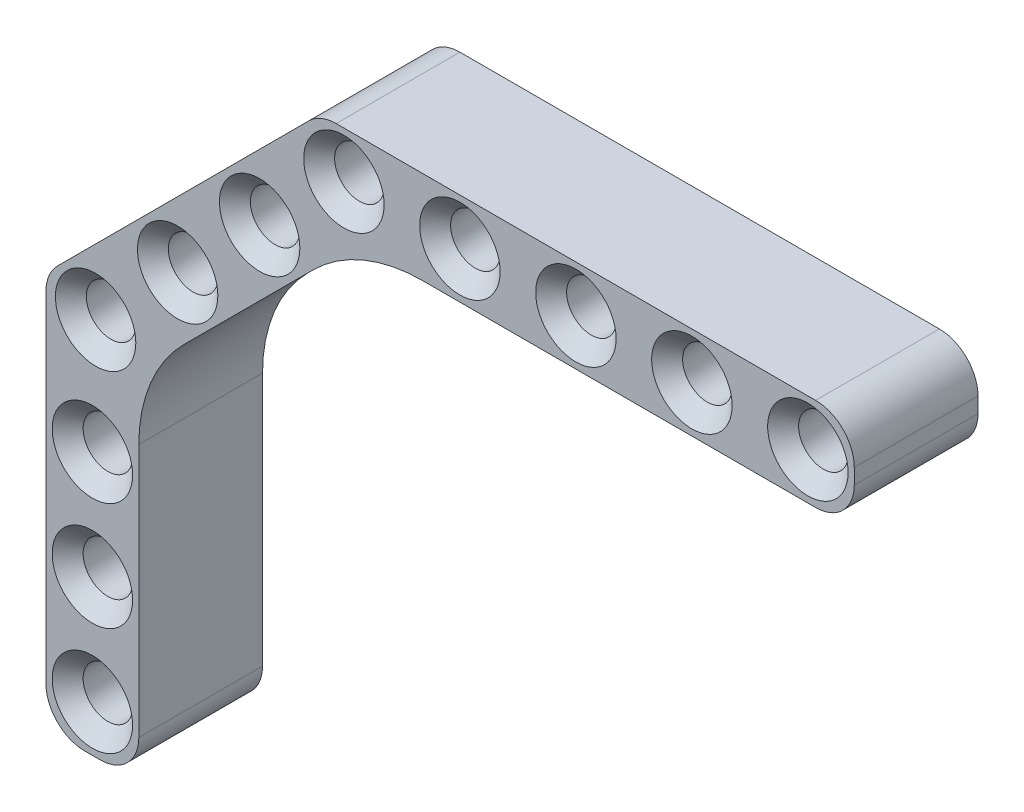
SolidWorks part; units mm, degrees
ref_plane "Front Plane" through (0, 0, 0) normal (0, 0, 1) x (1, 0, 0)
ref_plane "Top Plane" through (0, 0, 0) normal (0, 1, 0) x (1, 0, 0)
ref_plane "Right Plane" through (0, 0, 0) normal (1, 0, 0) x (0, 0, -1)
sketch "Sketch1" plane through (0, 0, 0) normal (0, 0, 1) x (1, 0, 0)
  line L1 (-0.5, 3) -> (30.5, 3)
  line L2 (-3, 0.5) -> (-3, -0.5)
  line L3 (-0.5, -3) -> (30.5, -3)
  line L4 (33, 0.5) -> (33, -0.5)
  circle A0 centre (0, 0) radius 1.6
  arc A1 (30.5, -3) -> (33, -0.5) centre (30.5, -0.5) ccw
  arc A2 (30.5, 3) -> (33, 0.5) centre (30.5, 0.5) cw
  arc A3 (-3, -0.5) -> (-0.5, -3) centre (-0.5, -0.5) ccw
  arc A4 (-0.5, 3) -> (-3, 0.5) centre (-0.5, 0.5) ccw
  circle A5 centre (7.5, 0) radius 1.6
  circle A6 centre (15, 0) radius 1.6
  circle A7 centre (22.5, 0) radius 1.6
  circle A8 centre (30, 0) radius 1.6
  point P8 (-3, 0)
  point P14 (-3, -3)
  point P17 (-3, 3)
  dimension "D1" = 3.2
  dimension "D4" = 2.5
  dimension "D2" = 6
  dimension "D3" = 3
  dimension "D6" = 7.5
  dimension "D5" = 5
extrude "Boss-Extrude1" add sketch "Sketch1" along normal blind 8
chamfer "Chamfer1" distance 1 angle 45 10 edges at (31.6, 0, 0) (31.6, 0, 8) (24.1, 0, 0) (24.1, 0, 8) (16.6, 0, 0) (16.6, 0, 8) (9.1, 0, 0) (9.1, 0, 8) (1.6, 0, 0) (1.6, 0, 8)
sketch "Sketch2" plane through (0, 0, 8) normal (0, 0, 1) x (1, 0, 0)
  line L0 (-2.2678, 2.2678) -> (-18.5292, -13.9937)
  line L1 (-18.5292, -17.5292) -> (-17.8221, -18.2363)
  line L2 (-14.2866, -18.2363) -> (0.9497, -3)
  line L4 (-0.5, -3) -> (30.5, -3) construction
  arc A0 (-0.5, 3) -> (-3, 0.5) centre (-0.5, 0.5) ccw construction
  circle A1 centre (-5.4477, -5.1548) radius 1.6
  circle A2 centre (-10.751, -10.4581) radius 1.6
  circle A3 centre (-16.0543, -15.7614) radius 1.6
  arc A4 (-18.5292, -13.9937) -> (-18.5292, -17.5292) centre (-16.7614, -15.7614) ccw
  arc A5 (-17.8221, -18.2363) -> (-14.2866, -18.2363) centre (-16.0543, -16.4685) ccw
  point P18 (-20.297, -15.7614)
  point P21 (-16.0543, -20.0041)
  arc M15 (-0.5, 3) -> (-3, 0.5) centre (-0.5, 0.5) ccw
  line M16 (-3, 0.5) -> (-3, -0.5)
  arc M17 (-3, -0.5) -> (-0.5, -3) centre (-0.5, -0.5) ccw
  line M18 (-0.5, -3) -> (30.5, -3)
  dimension "D3" = 3.2
  dimension "D8" = 2.5
  dimension "D1" = 6
  dimension "D2" = 45
  dimension "D4" = 3
  dimension "D5" = 7.5
  dimension "D7" = 3
  dimension "D6" = 3
extrude "Boss-Extrude3" add sketch "Sketch2" against normal blind 8 contours L1 A5 L2 L0 A4 A1 A2 A3 M18 M17 M16 M15
fillet "Fillet1" radius 10 1 edges at (0.9497, -3, 4)
chamfer "Chamfer2" distance 1 angle 45 6 edges at (-14.4543, -15.7614, 8) (-14.4543, -15.7614, 0) (-9.151, -10.4581, 8) (-9.151, -10.4581, 0) (-3.8477, -5.1548, 8) (-3.8477, -5.1548, 0)
sketch "Sketch3" plane through (0, 0, 8) normal (0, 0, 1) x (1, 0, 0)
  line L0 (-14.2866, -18.2363) -> (-1.9792, -5.9289) construction
  line L2 (-19.2614, -15.7614) -> (-19.2614, -37.7614)
  line L3 (-16.7614, -40.2614) -> (-15.7614, -40.2614)
  line L4 (-13.2614, -17.2112) -> (-13.2614, -37.7614)
  arc A0 (-18.5292, -13.9937) -> (-18.5292, -17.5292) centre (-16.7614, -15.7614) ccw construction
  circle A1 centre (-16.2614, -23.2614) radius 1.6
  circle A2 centre (-16.0543, -15.7614) radius 1.6 construction
  circle A3 centre (-16.2614, -30.2614) radius 1.6
  circle A4 centre (-16.2614, -37.2614) radius 1.6
  arc A5 (-19.2614, -37.7614) -> (-16.7614, -40.2614) centre (-16.7614, -37.7614) ccw
  arc A6 (-15.7614, -40.2614) -> (-13.2614, -37.7614) centre (-15.7614, -37.7614) ccw
  point P14 (-16.2614, -40.2614)
  point P20 (-19.2614, -40.2614)
  point P23 (-13.2614, -40.2614)
  arc M22 (-18.5292, -13.9937) -> (-18.5292, -17.5292) centre (-16.7614, -15.7614) ccw
  line M23 (-18.5292, -17.5292) -> (-17.8221, -18.2363)
  arc M24 (-17.8221, -18.2363) -> (-14.2866, -18.2363) centre (-16.0543, -16.4685) ccw
  line M25 (-14.2866, -18.2363) -> (-1.9792, -5.9289)
  dimension "D3" = 3.2
  dimension "D6" = 2.5
  dimension "D1" = 6
  dimension "D2" = 7.5
  dimension "D5" = 3
  dimension "D4" = 3
extrude "Boss-Extrude4" add sketch "Sketch3" against normal blind 8 contours L3 A6 L4 L2 A5 A1 A3 A4 M25 M24 M23 M22
chamfer "Chamfer5" distance 1 angle 45 6 edges at (-14.6614, -23.2614, 8) (-14.6614, -23.2614, 0) (-14.6614, -30.2614, 8) (-14.6614, -30.2614, 0) (-14.6614, -37.2614, 8) (-14.6614, -37.2614, 0)
fillet "Fillet2" radius 10 1 edges at (-13.2614, -17.2112, 4)
